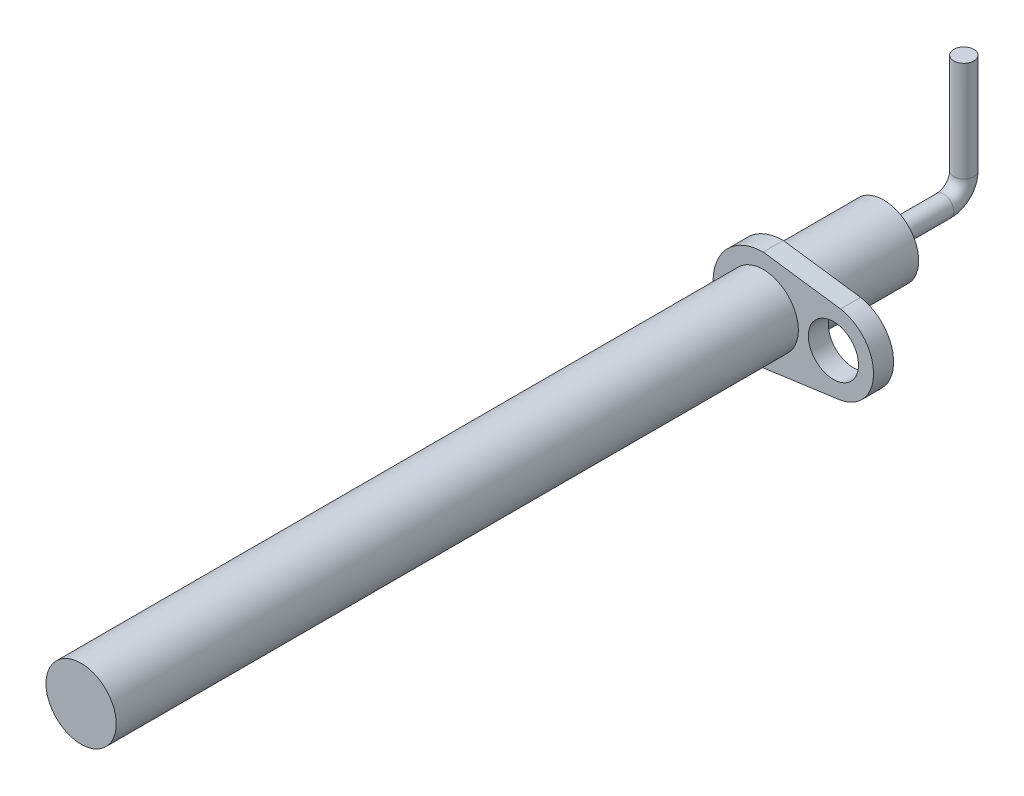
SolidWorks part; units mm, degrees
ref_plane "Front Plane" through (0, 0, 0) normal (0, 0, 1) x (1, 0, 0)
ref_plane "Top Plane" through (0, 0, 0) normal (0, 1, 0) x (1, 0, 0)
ref_plane "Right Plane" through (0, 0, 0) normal (1, 0, 0) x (0, 0, -1)
sketch "Sketch1" plane through (0, 0, 0) normal (0, 0, 1) x (1, 0, 0)
  circle A0 centre (0, 0) radius 1.75
  dimension "D1" = 3.5
extrude "Boss-Extrude1" add sketch "Sketch1" along normal blind 40
ref_plane "Plane1" through (0, 0, 6) normal (0, 0, -1) x (-1, 0, 0)
sketch "Sketch16" plane through (0, 0, 6) normal (0, 0, -1) x (-1, 0, 0)
  line L0 (0, 2.5) -> (0, -2.5) construction
  line L1 (-5.5, 0) -> (2.5, 0) construction
  line L2 (-3.8516, 1.9689) -> (0, 2.5)
  line L3 (-3.8516, -1.9689) -> (0, -2.5)
  arc A0 (0, 2.5) -> (0, -2.5) centre (0, 0) cw
  circle A1 centre (0, 0) radius 1.75 construction
  arc A2 (-3.8516, 1.9689) -> (-3.8516, -1.9689) centre (-3.5, 0) ccw
  circle A3 centre (-3.5, 0) radius 1.25
  dimension "D1" = 2.5
  dimension "D3" = 2
  dimension "D4" = 2.5
  dimension "D2" = 8
extrude "Boss-Extrude2" add sketch "Sketch16" along normal blind 1 contours L2 A2 L3 A0 A3
sketch3d "3DSketch1"
  line L0 (0, 0, 0) -> (0, 0, -3)
  line L1 (0, 1, -4) -> (0, 6, -4)
  arc A0 (0, 0, -3) -> (0, 1, -4) centre (0, 1, -3) ccw
  point P6 (0, 0, -4)
  point P7 (1, 1, -3)
  dimension "D3" = 1
  dimension "D1" = 4
  dimension "D2" = 6
sweep "Sweep1" add path "3DSketch1" circular profile diameter 1 parameters "D3"=1
